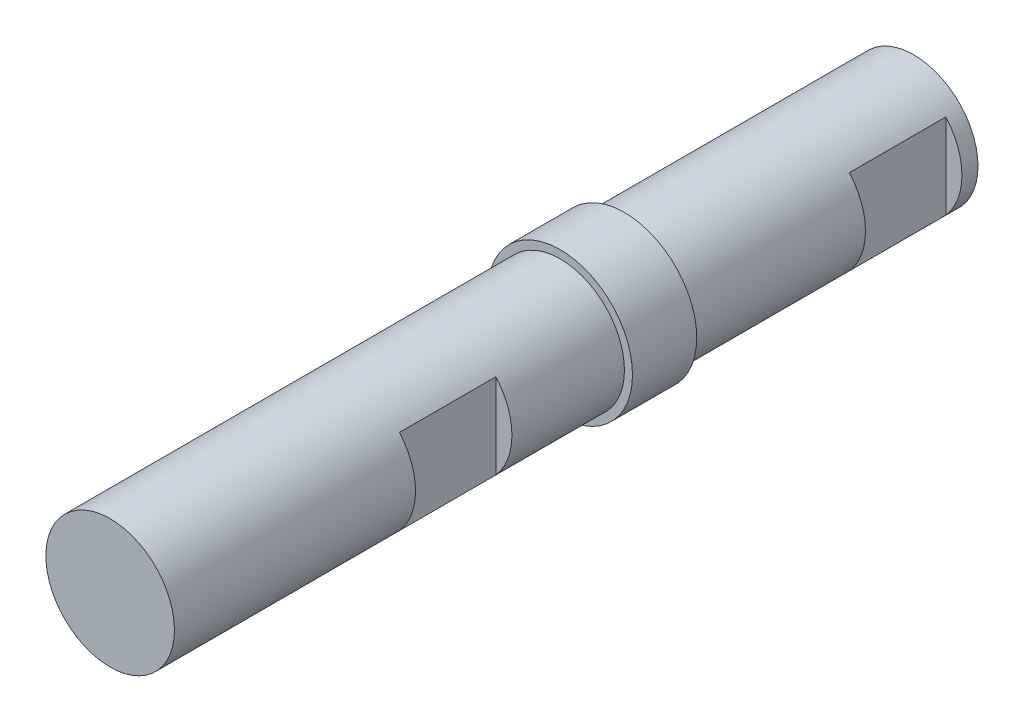
SolidWorks part; units mm, degrees
material "201 退火不鏽鋼 (SS)"
ref_plane "前基準面" through (0, 0, 0) normal (0, 0, 1) x (1, 0, 0)
ref_plane "上基準面" through (0, 0, 0) normal (0, 1, 0) x (1, 0, 0)
ref_plane "右基準面" through (0, 0, 0) normal (1, 0, 0) x (0, 0, -1)
sketch "草圖1" plane through (0, 0, 0) normal (0, 0, 1) x (1, 0, 0)
  circle A0 centre (0, 0) radius 4
  dimension "D1" = 8
extrude "填料-伸長1" add sketch "草圖1" along normal blind 18
sketch "草圖2" plane through (0, 0, 18) normal (0, 0, 1) x (1, 0, 0)
  circle A0 centre (0, 0) radius 4.5
  dimension "D1" = 9
extrude "填料-伸長2" add sketch "草圖2" along normal blind 4
sketch "草圖3" plane through (0, 0, 22) normal (0, 0, 1) x (1, 0, 0)
  circle A0 centre (0, 0) radius 4
  dimension "D1" = 8
extrude "填料-伸長3" add sketch "草圖3" along normal blind 28
ref_plane "平面1" through (4, 0, 0) normal (1, 0, 0) x (0, 0, -1)
sketch "草圖4" plane through (4, 0, 0) normal (1, 0, 0) x (0, 0, -1)
  line L0 (-50, 0) -> (-35, 0) construction
  line L1 (-50, 4) -> (-50, -4) construction
  line L3 (-35, 3) -> (-29, 3)
  line L4 (-35, 3) -> (-35, -3)
  line L5 (-35, -3) -> (-29, -3)
  line L6 (-29, 3) -> (-29, -3)
  point P9 (-35, 0)
  dimension "D1" = 15
  dimension "D2" = 6
  dimension "D3" = 6
extrude "除料-伸長1" cut sketch "草圖4" against normal blind 1
ref_plane "平面2" through (4, 0, 0) normal (1, 0, 0) x (0, 0, -1)
sketch "草圖5" plane through (4, 0, 0) normal (1, 0, 0) x (0, 0, -1)
  line L0 (0, 0) -> (-1, 0) construction
  line L2 (-1, 3) -> (-7, 3)
  line L3 (-1, 3) -> (-1, -3)
  line L4 (-1, -3) -> (-7, -3)
  line L5 (-7, 3) -> (-7, -3)
  point P8 (-1, 0)
  dimension "D1" = 1
  dimension "D2" = 6
  dimension "D3" = 6
extrude "除料-伸長2" cut sketch "草圖5" against normal blind 1
